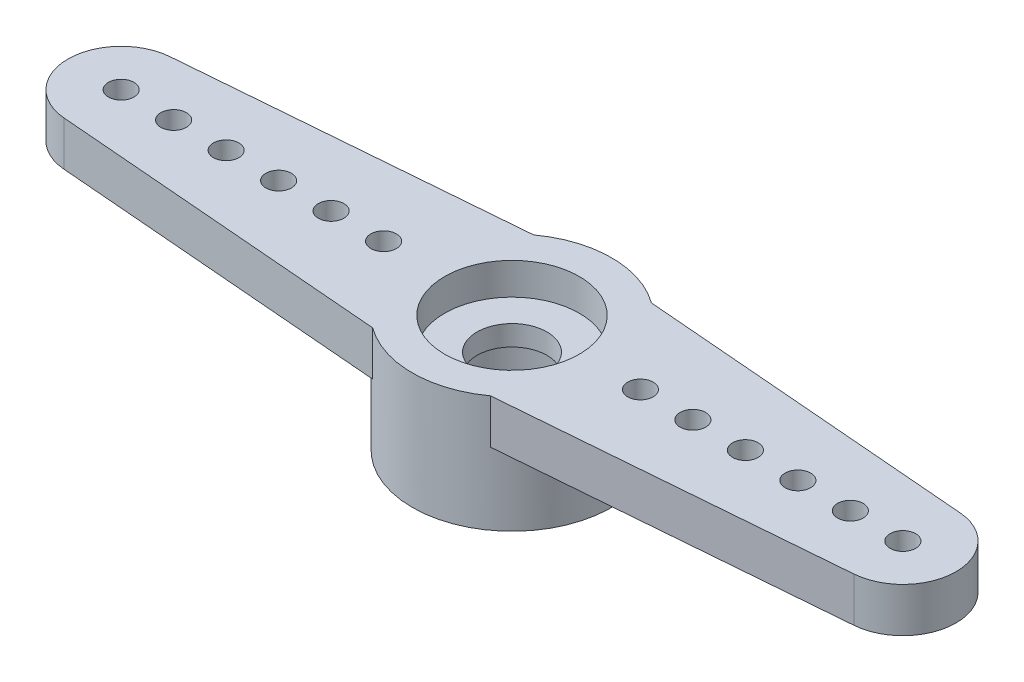
SolidWorks part; units mm, degrees
material "Nylon 101"
ref_plane "Front Plane" through (0, 0, 0) normal (0, 0, 1) x (1, 0, 0)
ref_plane "Top Plane" through (0, 0, 0) normal (0, 1, 0) x (1, 0, 0)
ref_plane "Right Plane" through (0, 0, 0) normal (1, 0, 0) x (0, 0, -1)
sketch "Sketch18" plane through (0, 0, 0) normal (0, 1, 0) x (1, 0, 0)
  line L0 (-16.1163, 0) -> (3.6195, 0) construction
  line L1 (-14.3431, 1.924) -> (-2.1374, 2.921)
  line L2 (-14.3431, -1.924) -> (-2.1374, -2.921)
  line L3 (2.1374, 2.921) -> (14.3431, 1.924)
  line L4 (14.3431, -1.924) -> (2.1374, -2.921)
  line L5 (0, 0) -> (0, 5.9555) construction
  arc A0 (-2.1374, -2.921) -> (2.1374, -2.921) centre (0, 0) ccw
  arc A1 (-14.3431, 1.924) -> (-14.3431, -1.924) centre (-14.1859, 0) ccw
  arc A2 (14.3431, 1.924) -> (14.3431, -1.924) centre (14.1859, 0) cw
  arc A3 (2.1374, 2.921) -> (-2.1374, 2.921) centre (0, 0) ccw
  dimension "D1" = 1.9304
  dimension "D2" = 3.6195
  dimension "D3" = 19.7358
  dimension "D4" = 5.842
extrude "Extrude17" add sketch "Sketch18" along normal blind 1.6129
sketch "Sketch19" plane through (0, 1.6129, 0) normal (0, 1, 0) x (1, 0, 0)
  circle A0 centre (0, 0) radius 3.6195
  arc A1 (-2.1374, -2.921) -> (2.1374, -2.921) centre (0, 0) ccw construction
extrude "Extrude19" add sketch "Sketch19" against normal blind 4.2291
sketch "Sketch20" plane through (0, 1.6129, 0) normal (0, 1, 0) x (1, 0, 0)
  line L0 (-14.1859, 0) -> (-12.2809, 0) construction
  line L1 (-12.2809, 0) -> (-10.3759, 0) construction
  line L2 (-10.3759, 0) -> (-8.4709, 0) construction
  line L3 (-8.4709, 0) -> (-6.5659, 0) construction
  line L4 (-6.5659, 0) -> (-4.6609, 0) construction
  line L5 (-4.6609, 0) -> (-2.7559, 0) construction
  line L6 (-2.7559, 0) -> (0, 0) construction
  circle A0 centre (-14.1859, 0) radius 0.4636
  circle A1 centre (0, 0) radius 1.27
  circle A3 centre (-4.6609, 0) radius 0.4636
  circle A4 centre (-6.5659, 0) radius 0.4636
  circle A5 centre (-8.4709, 0) radius 0.4636
  circle A6 centre (-10.3759, 0) radius 0.4636
  circle A7 centre (-12.2809, 0) radius 0.4636
  dimension "D1" = 0.9271
  dimension "D3" = 2.54
  dimension "D2" = 1.905
extrude "Extrude20" cut sketch "Sketch20" against normal through all
mirror "Mirror1" about plane through (0, 0, 0) normal (1, 0, 0) of "Extrude20"
sketch "Sketch21" plane through (0, 1.6129, 0) normal (0, 1, 0) x (1, 0, 0)
  circle A0 centre (0, 0) radius 2.4447
  dimension "D1" = 4.8895
extrude "Extrude21" cut sketch "Sketch21" against normal blind 1.1557
sketch "Sketch22" plane through (0, -2.6162, 0) normal (0, -1, 0) x (1, 0, 0)
  circle A0 centre (0, 0) radius 2.286
  dimension "D1" = 4.572
extrude "Extrude22" cut sketch "Sketch22" against normal blind 2.3368
